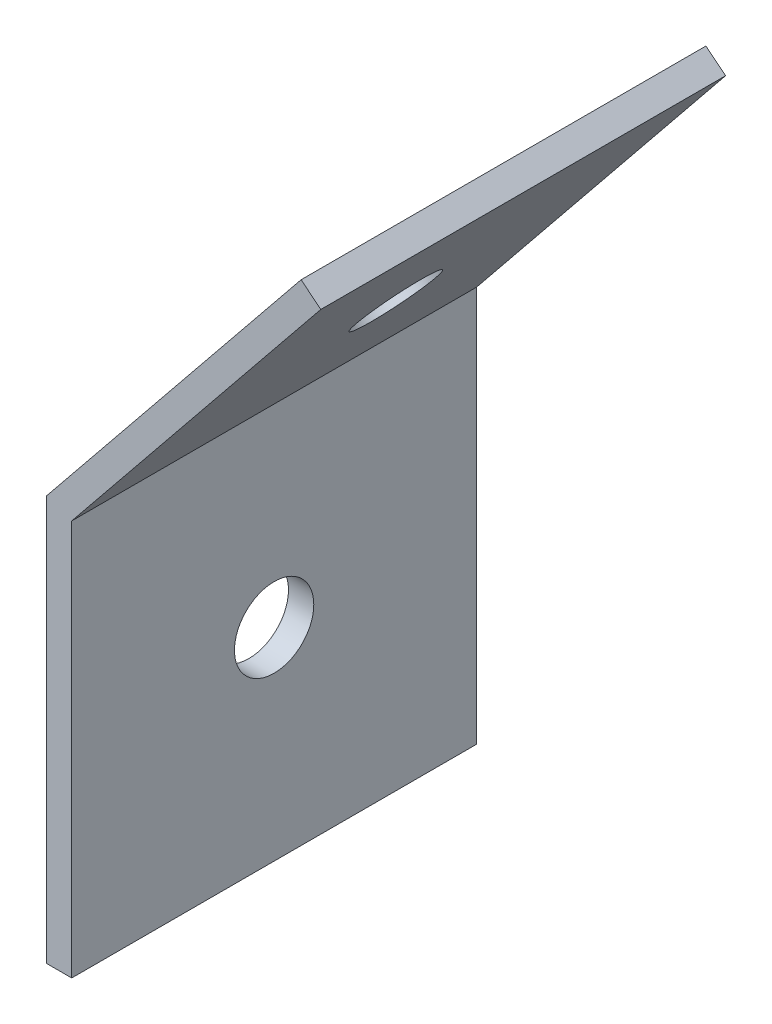
SolidWorks part; units mm, degrees
ref_plane "Front Plane" through (0, 0, 0) normal (0, 0, 1) x (1, 0, 0)
ref_plane "Top Plane" through (0, 0, 0) normal (0, 1, 0) x (1, 0, 0)
ref_plane "Right Plane" through (0, 0, 0) normal (1, 0, 0) x (0, 0, -1)
sketch "Sketch1" plane through (0, 0, 0) normal (0, 0, 1) x (1, 0, 0)
  line L0 (0, 0) -> (15.982, 19.7417)
  line L1 (0, 0) -> (0, -25.4)
  dimension "D1" = 25.4
extrude "Extrude-Thin1" add sketch "Sketch1" against normal blind 25.4 thin
ref_plane "Plane1" through (0, 0, 0) normal (-0.3337, -0.9427, 0) x (-0.9427, 0.3337, 0)
hole_wizard "#9 (0.196) Diameter Hole1" positions "Sketch4" profile "Sketch5" hole size "#9" standard "ANSI Inch" end condition up to next
sketch "Sketch4" plane through (1.2339, -0.9989, 0) normal (0.7772, -0.6292, 0) x (0, 0, -1)
  line L0 (25.4, 25.4) -> (25.4, 0.562) construction
  line L1 (25.4, 25.4) -> (0, 25.4) construction
  point P0 (12.7, 12.7)
  dimension "D1" = 12.7
  dimension "D2" = 12.7
sketch "Sketch5" plane through (9.2249, 8.872, -12.7) normal (0, 0, 1) x (0.6292, 0.7772, 0)
  line L0 (0, 0) -> (0, 1.5885)
  line L1 (0, 1.5885) -> (2.4892, 1.5885)
  line L2 (2.4892, 1.5885) -> (2.4892, 0)
  line L5 (2.4892, 0) -> (0, 0)
  line L11 (0, -6.35) -> (0, 107.95) construction
  dimension "Thru Hole Dia." = 4.9784
  dimension "Thru Hole Depth" = 1.5885
mirror "Mirror1" about plane through (0, 0, 0) normal (-0.3337, -0.9427, 0) of "#9 (0.196) Diameter Hole1"
equation "\"Thick\"= \"in\""
